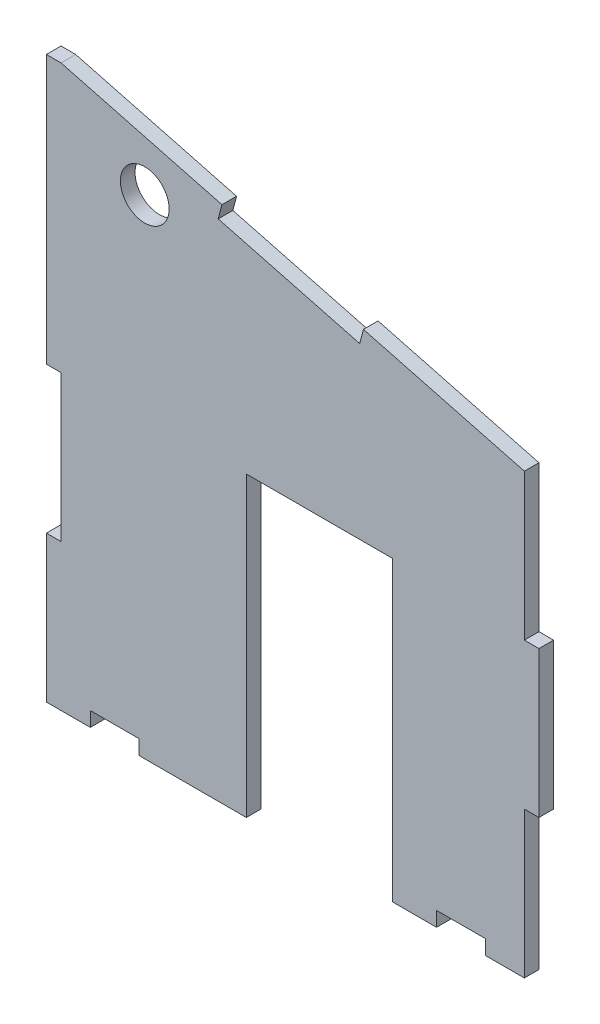
SolidWorks part; units mm, degrees
ref_plane "Front Plane" through (0, 0, 0) normal (0, 0, 1) x (1, 0, 0)
ref_plane "Top Plane" through (0, 0, 0) normal (0, 1, 0) x (1, 0, 0)
ref_plane "Right Plane" through (0, 0, 0) normal (1, 0, 0) x (0, 0, -1)
sketch "Model" plane through (0, 0, 0) normal (0, 0, 1) x (1, 0, 0)
  line L1 (352.6902, 199.1238) -> (352.6902, 169.1238)
  line L2 (322.6902, 139.1238) -> (322.6902, 200.1238)
  line L3 (322.6902, 200.1238) -> (292.6902, 200.1238)
  line L4 (292.6902, 200.1238) -> (292.6902, 139.1238)
  line L5 (349.6902, 229.1238) -> (251.6902, 229.1238) construction
  line L10 (254.6902, 199.1238) -> (254.6902, 254.1238) construction
  line L13 (349.6902, 229.1238) -> (316.6963, 237.8064)
  line L16 (251.6902, 199.1238) -> (251.6902, 254.1238) construction
  line L19 (251.6902, 254.1238) -> (254.6902, 254.1238)
  line L20 (348.9267, 226.2225) -> (253.9267, 251.2225) construction
  line L21 (349.6902, 139.1238) -> (341.6902, 139.1238)
  line L22 (349.6902, 229.1238) -> (348.9267, 226.2225) construction
  line L23 (341.6902, 139.1238) -> (341.6902, 142.1238)
  line L29 (254.6902, 254.1238) -> (253.9267, 251.2225) construction
  line L34 (341.6902, 142.1238) -> (331.6902, 142.1238)
  line L39 (302.1902, 241.6238) -> (301.4267, 238.7225) construction
  line L40 (287.6841, 245.4412) -> (286.9206, 242.5399)
  line L44 (254.6902, 199.1238) -> (254.6902, 169.1238)
  line L45 (254.6902, 169.1238) -> (251.6902, 169.1238)
  line L47 (251.6902, 199.1238) -> (254.6902, 199.1238)
  line L48 (316.6963, 237.8064) -> (315.9328, 234.9051)
  line L49 (251.6902, 254.1238) -> (251.6902, 199.1238)
  line L54 (251.6902, 169.1238) -> (251.6902, 139.1238)
  line L55 (287.6841, 245.4412) -> (254.6902, 254.1238)
  line L56 (315.9328, 234.9051) -> (286.9206, 242.5399)
  line L57 (349.6902, 229.1238) -> (254.6902, 254.1238) construction
  line L58 (349.6902, 229.1238) -> (254.6902, 254.1238) construction
  line L59 (331.6902, 142.1238) -> (331.6902, 139.1238)
  line L60 (331.6902, 139.1238) -> (322.6902, 139.1238)
  line L61 (251.6902, 139.1238) -> (260.6902, 139.1238)
  line L62 (260.6902, 139.1238) -> (260.6902, 142.1238)
  line L63 (260.6902, 142.1238) -> (270.6902, 142.1238)
  line L64 (270.6902, 142.1238) -> (270.6902, 139.1238)
  line L65 (270.6902, 139.1238) -> (292.6902, 139.1238)
  line L312 (292.6902, 139.1238) -> (251.6902, 139.1238) construction
  line L335 (349.6902, 229.1238) -> (349.6902, 199.1238)
  line L336 (349.6902, 199.1238) -> (352.6902, 199.1238)
  line L354 (352.6902, 169.1238) -> (349.6902, 169.1238)
  line L355 (349.6902, 169.1238) -> (349.6902, 139.1238)
  line L356 (349.6902, 139.1238) -> (322.6902, 139.1238) construction
  circle A0 centre (271.8599, 239.265) radius 5
  point P6 (265.1905, 254.1238)
  point P7 (178.1905, 232.3738)
  point P9 (352.1905, 232.3738)
  point P18 (341.6902, 140.6238)
  point P348 (181.6279, 229.1238)
  dimension "D5" = 10
  dimension "D22" = 27
  dimension "D4" = 30
  dimension "D6" = 3
  dimension "D7" = 3
  dimension "D8" = 10
  dimension "D9" = 30
  dimension "D10" = 30
  dimension "D11" = 25
  dimension "D12" = 30
  dimension "D13" = 61
  dimension "D14" = 25
  dimension "D15" = 3
  dimension "D16" = 8
  dimension "D17" = 95
  dimension "D18" = 15
  dimension "D19" = 15
  dimension "D20" = 3
  dimension "D21" = 10
  dimension "D23" = 9
  dimension "D27" = 3
  dimension "D29" = 30
  dimension "D30" = 30
extrude "Boss-Extrude1" add sketch "Model" along normal blind 3
